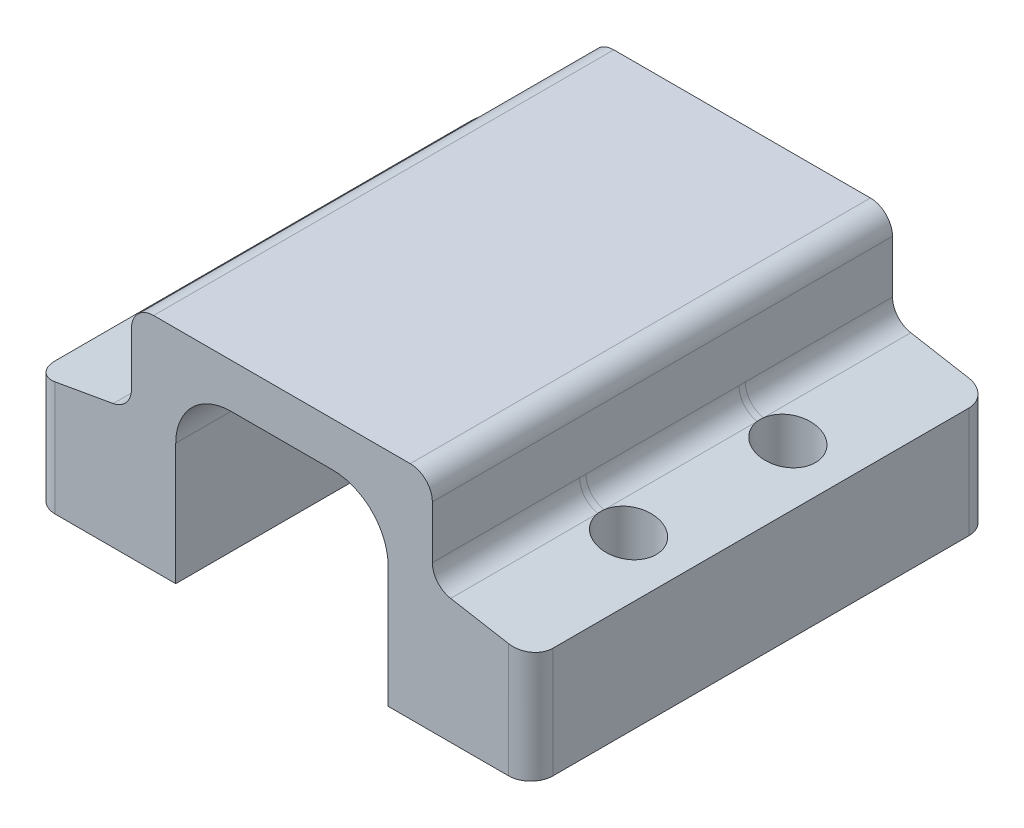
SolidWorks part; units mm, degrees
ref_plane "Front Plane" through (0, 0, 0) normal (0, 0, 1) x (1, 0, 0)
ref_plane "Top Plane" through (0, 0, 0) normal (0, 1, 0) x (1, 0, 0)
ref_plane "Right Plane" through (0, 0, 0) normal (1, 0, 0) x (0, 0, -1)
sketch "Sketch1" plane through (0, 0, 0) normal (0, 0, 1) x (1, 0, 0)
  line L0 (-92.6582, 0) -> (89.2369, 0) construction
  line L2 (-6.096, 10.16) -> (6.096, 10.16)
  line L3 (6.096, 10.16) -> (6.096, 0)
  line L4 (-6.096, 0) -> (6.096, 0) construction
  line L5 (8.89, 6.35) -> (14.2875, 6.35) construction
  line L6 (14.2875, 6.35) -> (14.2875, 0)
  line L7 (14.2875, 0) -> (6.096, 0)
  line L8 (8.636, 7.3465) -> (8.636, 12.7)
  line L9 (8.636, 12.7) -> (-8.636, 12.7)
  line L10 (0, 0) -> (0, 31.7739) construction
  line L13 (-8.636, 7.3465) -> (-8.636, 12.7)
  line L14 (-8.89, 6.35) -> (-14.2875, 6.35) construction
  line L15 (-14.2875, 6.35) -> (-14.2875, 0)
  line L16 (-14.2875, 0) -> (-6.096, 0)
  line L17 (-6.096, 10.16) -> (-6.096, 0)
  line L18 (14.2875, 6.35) -> (8.636, 7.3465)
  line L19 (-14.2875, 6.35) -> (-8.636, 7.3465)
  point P5 (0, 0)
  point P16 (0, 12.7)
  point P24 (0, 10.16)
  dimension "D1" = 10.16
  dimension "D2" = 2.54
  dimension "D3" = 12.192
  dimension "D4" = 12.7
  dimension "D5" = 6.35
  dimension "D7" = 28.575
  dimension "D8" = 10
  dimension "D9" = 10
extrude "Boss-Extrude1" add sketch "Sketch1" against normal blind 22.86 and the other way blind 3.556
sketch "Sketch2" plane through (0, 0, 3.556) normal (0, 0, 1) x (1, 0, 0)
  line L0 (6.096, 10.16) -> (6.096, 0) construction
  line L1 (-6.096, 10.16) -> (6.096, 10.16) construction
  line L2 (6.096, 6.985) -> (6.096, 0) construction
  line L3 (-6.096, 10.16) -> (2.921, 10.16) construction
  line L4 (2.921, 10.16) -> (6.096, 10.16)
  line L5 (6.096, 10.16) -> (6.096, 6.985)
  line L6 (0, 0) -> (0, 17.4905) construction
  line L7 (-6.096, 10.16) -> (-6.096, 6.985)
  line L8 (-2.921, 10.16) -> (-6.096, 10.16)
  arc A0 (6.096, 6.985) -> (2.921, 10.16) centre (2.921, 6.985) ccw
  arc A1 (-6.096, 6.985) -> (-2.921, 10.16) centre (-2.921, 6.985) cw
  dimension "D1" = 3.175
extrude "Boss-Extrude2" add sketch "Sketch2" against normal blind 13.462
sketch "Sketch3" plane through (0, 0, -9.906) normal (0, 0, 1) x (1, 0, 0)
  line L2 (-6.096, 10.16) -> (-6.096, 6.985)
  line L3 (-2.921, 10.16) -> (-6.096, 10.16)
  line L4 (-6.096, 10.16) -> (-6.096, 6.985)
  line L5 (-2.921, 10.16) -> (-6.096, 10.16)
  line L6 (6.096, 10.16) -> (2.921, 10.16)
  line L7 (6.096, 6.985) -> (6.096, 10.16)
  line L8 (6.096, 10.16) -> (2.921, 10.16) construction
  line L9 (6.096, 6.985) -> (6.096, 10.16) construction
  arc A1 (-2.921, 10.16) -> (-6.096, 6.985) centre (-2.921, 6.985) ccw
  arc A2 (-2.921, 10.16) -> (-6.096, 6.985) centre (-2.921, 6.985) ccw
  arc A3 (6.096, 6.985) -> (2.921, 10.16) centre (2.921, 6.985) ccw
  arc A4 (6.096, 6.985) -> (2.921, 10.16) centre (2.921, 6.985) ccw construction
  dimension "D1" = 0
  dimension "D2" = 0
extrude "Boss-Extrude3" add sketch "Sketch3" against normal blind 1.905 from offset 1.27 offset against normal yes
sketch "Sketch4" plane through (0, 0, -13.081) normal (0, 0, 1) x (1, 0, 0)
  line L2 (-6.096, 10.16) -> (-6.096, 6.985)
  line L3 (-2.921, 10.16) -> (-6.096, 10.16)
  line L4 (-6.096, 10.16) -> (-6.096, 6.985)
  line L5 (-2.921, 10.16) -> (-6.096, 10.16)
  arc A1 (-2.921, 10.16) -> (-6.096, 6.985) centre (-2.921, 6.985) ccw
  arc A2 (-2.921, 10.16) -> (-6.096, 6.985) centre (-2.921, 6.985) ccw
  dimension "D1" = 0
sketch "Sketch5" plane through (0, 0, 0) normal (0, 1, 0) x (1, 0, 0)
  line L0 (-5.9055, 22.0472) -> (5.9055, 22.0472)
  line L1 (5.9055, 22.0472) -> (5.9055, 22.86)
  line L2 (5.9055, 22.86) -> (-5.9055, 22.86)
  line L3 (-5.9055, 22.86) -> (-5.9055, 22.0472)
  line L5 (-5.9055, 17.018) -> (5.9055, 17.018)
  line L6 (-5.9055, 17.018) -> (-5.9055, 17.8308)
  line L7 (-5.9055, 17.8308) -> (5.9055, 17.8308)
  line L8 (5.9055, 17.018) -> (5.9055, 17.8308)
  line L9 (-5.9055, 13.8176) -> (5.9055, 13.8176)
  line L10 (-5.9055, 13.8176) -> (-5.9055, 14.6304)
  line L11 (-5.9055, 14.6304) -> (5.9055, 14.6304)
  line L12 (5.9055, 13.8176) -> (5.9055, 14.6304)
  line L13 (-5.9055, 13.8176) -> (5.9055, 13.8176)
  line L14 (-5.9055, 13.8176) -> (-5.9055, -1.27)
  line L15 (-5.9055, -1.27) -> (5.9055, -1.27)
  line L16 (5.9055, 13.8176) -> (5.9055, -1.27)
  line L17 (-6.096, 22.86) -> (6.096, 22.86) construction
  point P12 (0, 22.0472)
  dimension "D1" = 0.8128
  dimension "D2" = 11.811
  dimension "D3" = 5.842
  dimension "D4" = 4.0132
  dimension "D5" = 24.13
ref_plane "Plane1" through (0, 0, -5.08) normal (0, 0, 1) x (1, 0, 0)
sketch "Sketch6" plane through (0, 0, -5.08) normal (0, 0, 1) x (1, 0, 0)
  line L0 (13.889, 6.4203) -> (8.636, 7.3465) construction
  line L1 (8.636, 7.3465) -> (9.0771, 9.8479) construction
  line L2 (9.0771, 9.8479) -> (14.33, 8.9217) construction
  line L3 (14.33, 8.9217) -> (13.889, 6.4203) construction
  line L4 (11.2625, 6.8834) -> (11.2625, -1.27) construction
  line L5 (6.096, 0) -> (14.2875, 0) construction
  line L6 (8.636, 7.3465) -> (8.636, 12.7) construction
  line L8 (11.2625, -1.27) -> (12.85, -1.27)
  line L9 (12.85, -1.27) -> (12.85, 6.6035)
  line L10 (12.85, 6.6035) -> (11.2625, 6.8834) construction
  line L11 (11.2625, 6.8834) -> (11.2625, -1.27)
  line L12 (11.2625, -1.27) -> (11.2625, -5.0048) construction
  line L13 (8.636, 7.3465) -> (8.636, 6.35) construction
  line L14 (8.636, 6.35) -> (14.2875, 6.35) construction
  line L15 (14.2875, 6.35) -> (8.636, 7.3465) construction
  line L16 (12.85, 9.4234) -> (12.85, 6.6035)
  line L17 (11.2625, 6.8834) -> (11.2625, 9.4234)
  line L18 (11.2625, 9.4234) -> (12.85, 9.4234)
  dimension "D1" = 5.334
  dimension "D2" = 10
  dimension "D3" = 2.54
  dimension "D4" = 3.175
  dimension "D5" = 1.27
  dimension "D6" = 2.54
revolve "Cut-Revolve1" cut sketch "Sketch6" angle 360 about L12
mirror "Mirror1" about plane through (0, 0, 0) normal (1, 0, 0) of "Cut-Revolve1"
ref_plane "Plane2" through (0, 0, -9.652) normal (0, 0, 1) x (1, 0, 0)
mirror "Mirror2" about plane through (0, 0, -9.652) normal (0, 0, 1) of "Mirror1", "Cut-Revolve1"
fillet "Fillet1" radius 1.27 8 edges at (-8.636, 12.7, -9.652) (8.636, 12.7, -9.652) (-14.2875, 3.175, -22.86) (-14.2875, 3.175, 3.556) (14.2875, 3.175, -22.86) (14.2875, 3.175, 3.556) (-8.636, 7.3465, -9.652) (8.636, 7.3465, -9.652)
sketch "Sketch7" plane through (0, 0, 0) normal (0, 1, 0) x (1, 0, 0)
extrude "Boss-Extrude4" add sketch "Sketch4" against normal blind 8.509
ref_plane "Plane3" through (0, 0, -12.446) normal (0, 0, 1) x (1, 0, 0)
sketch "Sketch9" plane through (0, 0, -12.446) normal (0, 0, 1) x (1, 0, 0)
  line L0 (-6.096, 6.985) -> (-5.9873, 7.8086)
  line L1 (-5.9873, 7.8086) -> (-5.6758, 8.5634)
  line L2 (-5.6758, 8.5634) -> (-5.1661, 9.2301)
  line L3 (-5.1661, 9.2301) -> (-4.513, 9.732)
  line L4 (-4.513, 9.732) -> (-3.747, 10.0507)
  line L5 (-3.747, 10.0507) -> (-2.921, 10.16)
  line L6 (-2.921, 10.16) -> (-6.096, 10.16)
  line L7 (-6.096, 10.16) -> (-6.096, 6.985)
  arc A0 (-2.921, 10.16) -> (-6.096, 6.985) centre (-2.921, 6.985) ccw construction
extrude "Cut-Extrude1" cut sketch "Sketch9" against normal blind 7.874
